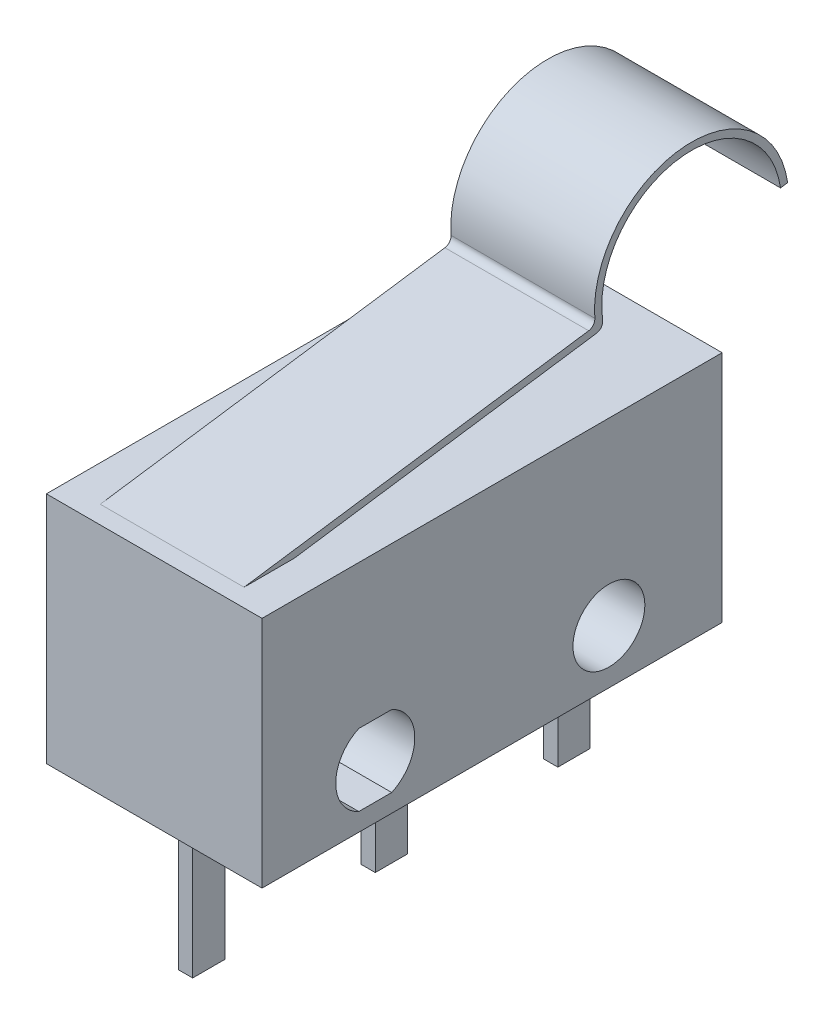
SolidWorks part; units mm, degrees
ref_plane "Front Plane" through (0, 0, 0) normal (0, 0, 1) x (1, 0, 0)
ref_plane "Top Plane" through (0, 0, 0) normal (0, 1, 0) x (1, 0, 0)
ref_plane "Right Plane" through (0, 0, 0) normal (1, 0, 0) x (0, 0, -1)
sketch "Sketch1" plane through (0, 0, 0) normal (1, 0, 0) x (0, 0, -1)
  line L0 (-3.25, -1.75) -> (3.25, -1.75) construction
  line L1 (6.4, 3.25) -> (-6.4, 3.25)
  line L2 (6.4, 3.25) -> (6.4, -3.25)
  line L3 (6.4, -3.25) -> (-6.4, -3.25)
  line L4 (-6.4, 3.25) -> (-6.4, -3.25)
  line L5 (6.4, 3.25) -> (-6.4, -3.25) construction
  line L6 (6.4, -3.25) -> (-6.4, 3.25) construction
  line L7 (-3.7083, -0.75) -> (-2.7917, -0.75)
  line L8 (-3.7083, -2.75) -> (-2.7917, -2.75)
  arc A0 (-3.7083, -0.75) -> (-3.7083, -2.75) centre (-3.25, -1.75) ccw
  circle A1 centre (3.25, -1.75) radius 1
  arc A2 (-2.7917, -2.75) -> (-2.7917, -0.75) centre (-3.25, -1.75) ccw
  point P0 (0, 0)
  point P14 (0, -1.75)
  dimension "D3" = 2.2
  dimension "D4" = 2
  dimension "D1" = 12.8
  dimension "D2" = 6.5
  dimension "D5" = 5
  dimension "D6" = 2
  dimension "D7" = 6.5
extrude "Boss-Extrude1" add sketch "Sketch1" along normal mid plane 6
sketch "Sketch3" plane through (0, 0, 0) normal (1, 0, 0) x (0, 0, -1)
  line L0 (-5.53, -3.25) -> (-5.53, -7.25)
  line L1 (-6.4, -3.25) -> (6.4, -3.25) construction
  line L2 (-5.53, -7.25) -> (-4.63, -7.25)
  line L3 (-4.63, -7.25) -> (-4.63, -3.25)
  line L4 (-4.63, -3.25) -> (-5.53, -3.25)
  line L5 (-4.63, -5.25) -> (0.45, -5.25) construction
  line L6 (0.45, -3.25) -> (-0.45, -3.25)
  line L7 (0.45, -3.25) -> (0.45, -7.25)
  line L8 (0.45, -7.25) -> (-0.45, -7.25)
  line L9 (-0.45, -3.25) -> (-0.45, -7.25)
  line L10 (4.63, -3.25) -> (5.53, -3.25)
  line L11 (4.63, -3.25) -> (4.63, -7.25)
  line L12 (4.63, -7.25) -> (5.53, -7.25)
  line L13 (5.53, -3.25) -> (5.53, -7.25)
  line L14 (-0.45, -5.25) -> (4.63, -5.25) construction
  point P18 (0, -7.25)
  dimension "D1" = 5.08
  dimension "D2" = 0.9
  dimension "D3" = 4
extrude "Boss-Extrude2" add sketch "Sketch3" along normal mid plane 0.4
sketch "Sketch4" plane through (0, 0, 0) normal (1, 0, 0) x (0, 0, -1)
  line L0 (-5.9, 3.25) -> (3.8778, 4.6637)
  line L1 (6.4, 3.25) -> (-6.4, 3.25) construction
  line L2 (9.2222, 5.4363) -> (9.0243, 5.4077)
  line L3 (4.1123, 4.4955) -> (-4.5023, 3.25)
  line L4 (-4.5023, 3.25) -> (-5.9, 3.25)
  line L5 (4.4677, 7.75) -> (9.5638, 7.75) construction
  arc A0 (3.8778, 4.6637) -> (9.2222, 5.4363) centre (6.55, 5.05) cw
  arc A1 (9.0243, 5.4077) -> (4.1123, 4.4955) centre (6.55, 5.05) ccw
  circle A2 centre (3.25, -1.75) radius 1 construction
  dimension "D1" = 2.5
  dimension "D2" = 3.3
  dimension "D3" = 0.2
  dimension "D4" = 0.2
  dimension "D5" = 9.5
  dimension "D6" = 0.5
extrude "Boss-Extrude3" add sketch "Sketch4" along normal mid plane 4
sketch "Sketch5" plane through (0, 0, 0) normal (1, 0, 0) x (0, 0, -1)
  line L0 (6.4, 3.25) -> (-6.4, 3.25) construction
  line L1 (-2.48, 3.25) -> (-1.82, 3.25)
  arc A0 (-1.82, 3.25) -> (-2.48, 3.25) centre (-2.15, 3.25) ccw
  circle A1 centre (3.25, -1.75) radius 1 construction
  dimension "D2" = 0.33
  dimension "D1" = 5.4
fillet "Fillet1" radius 0.2 2 edges at (0, 4.4955, -4.1123) (0, 4.6637, -3.8778)
extrude "Boss-Extrude5" add sketch "Sketch5" along normal mid plane 1
